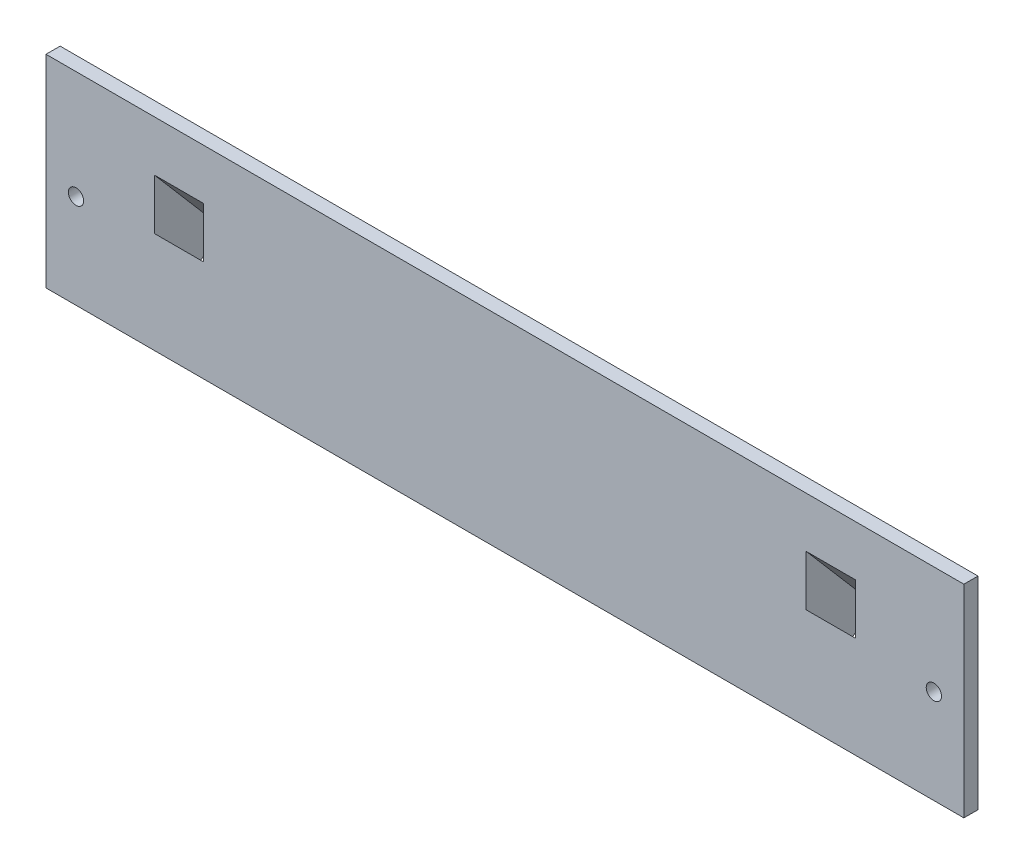
SolidWorks part; units mm, degrees
ref_plane "Alzado" through (0, 0, 0) normal (0, 0, 1) x (1, 0, 0)
ref_plane "Planta" through (0, 0, 0) normal (0, 1, 0) x (1, 0, 0)
ref_plane "Vista lateral" through (0, 0, 0) normal (1, 0, 0) x (0, 0, -1)
sketch "Croquis1" plane through (0, 0, 0) normal (0, 0, 1) x (1, 0, 0)
  line L0 (-97.5, 0) -> (97.5, 0)
  line L1 (97.5, 0) -> (97.5, 38)
  line L2 (97.5, 38) -> (-97.5, 38)
  line L3 (0, 0) -> (0, 28.0598) construction
  line L4 (-97.5, 0) -> (-97.5, 38)
  circle A2 centre (91.125, 15) radius 1.625
  circle A3 centre (-91.125, 15) radius 1.625
  point P13 (0, 38)
  point P14 (0, 0)
  dimension "D1" = 3.25
  dimension "D2" = 15
  dimension "D3" = 97.5
  dimension "D4" = 38
  dimension "D5" = 6.375
extrude "Saliente-Extruir1" add sketch "Croquis1" along normal blind 3
sketch "Croquis2" plane through (97.5, 0, 0) normal (1, 0, 0) x (0, 0, -1)
  line L7 (3.4296, 3.6779) -> (15.1854, 13.7539)
  line L9 (0, 0) -> (0, 38) construction
  line L10 (-3, 0) -> (0, 0) construction
  line L11 (15.1854, 13.7539) -> (0, 31.471)
  line L12 (0, 31.471) -> (0, 0.7384)
  line L13 (3.4296, 3.6779) -> (0, 0.7384)
  dimension "D1" = 40.6
  dimension "D2" = 20
extrude "Saliente-Extruir2" add sketch "Croquis2" against normal blind 16.5 from offset 20 offset against normal yes
sketch "Croquis3" plane through (0, 0.4257, 0.3649) normal (0, -0.7593, -0.6508) x (1, 0, 0)
  line L0 (61, -20.4805) -> (61, -0.4805) construction
  line L1 (64, -8.4805) -> (74.5, -8.4805)
  line L2 (64, -8.4805) -> (64, -15.4805)
  line L3 (64, -15.4805) -> (74.5, -15.4805)
  line L4 (74.5, -8.4805) -> (74.5, -15.4805)
  line L5 (61, -20.4805) -> (77.5, -20.4805) construction
  dimension "D1" = 10.5
  dimension "D2" = 3
  dimension "D3" = 5
  dimension "D4" = 7
extrude "Cortar-Extruir1" cut sketch "Croquis3" against normal through all
sketch "Croquis4" plane through (-97.5, 0, 0) normal (-1, 0, 0) x (0, 0, 1)
  line L0 (0, 0.7384) -> (-15.1854, 13.7539)
  line L1 (-15.1854, 13.7539) -> (0, 31.471)
  line L2 (0, 38) -> (0, 0) construction
  line L3 (0, 0.7384) -> (0, 31.471) construction
  line L4 (0, 31.471) -> (0, 0.7384)
extrude "Saliente-Extruir3" add sketch "Croquis4" against normal blind 16.5 from offset 20 offset against normal yes
sketch "Croquis5" plane through (0, 0.4257, 0.3649) normal (0, -0.7593, -0.6508) x (1, 0, 0)
  line L0 (-61, -20.4805) -> (-61, -0.4805) construction
  line L1 (-64, -15.4805) -> (-74.5, -15.4805)
  line L2 (-64, -15.4805) -> (-64, -8.4805)
  line L3 (-64, -8.4805) -> (-74.5, -8.4805)
  line L4 (-74.5, -15.4805) -> (-74.5, -8.4805)
  line L5 (64, -15.4805) -> (74.5, -15.4805) construction
  dimension "D1" = 3
  dimension "D2" = 10.5
  dimension "D3" = 7
extrude "Cortar-Extruir2" cut sketch "Croquis5" against normal through all
sketch "Croquis6" plane through (97.5, 0, 0) normal (1, 0, 0) x (0, 0, -1)
  line L0 (0, 0.7384) -> (15.1854, 13.7539)
  line L1 (15.1854, 13.7539) -> (0, 31.471)
  line L2 (0, 31.471) -> (0, 0.7384)
extrude "Saliente-Extruir4" add sketch "Croquis6" along normal blind 45 from offset 120 offset against normal yes
sketch "Croquis7" plane through (0, 0.4257, 0.3649) normal (0, -0.7593, -0.6508) x (1, 0, 0)
  line L0 (-22.5, -20.4805) -> (-22.5, -0.4805) construction
  circle A0 centre (-12.92, -10.4805) radius 8.25
  circle A1 centre (12.93, -10.4805) radius 8.25
  dimension "D1" = 16.5
  dimension "D2" = 25.85
  dimension "D3" = 9.58
extrude "Cortar-Extruir3" cut sketch "Croquis7" against normal through all
sketch "Croquis8" plane through (0, 0, 0) normal (0, -1, 0) x (1, 0, 0)
  line L1 (-97.5, 3) -> (97.5, 3)
  line L2 (-97.5, 3) -> (-97.5, 0)
  line L3 (-97.5, 0) -> (97.5, 0)
  line L4 (97.5, 3) -> (97.5, 0)
extrude "Saliente-Extruir5" add sketch "Croquis8" along normal blind 5
sketch "Croquis9" plane through (-22.5, 0, 0) normal (-1, 0, 0) x (0, 0, 1)
  line L0 (0, 0.7384) -> (-15.1854, 13.7539)
  line L1 (-15.1854, 13.7539) -> (0, 31.471)
  line L2 (0, 31.471) -> (0, 0.7384)
extrude "Cortar-Extruir4" cut sketch "Croquis9" against normal up to next
sketch "Croquis10" plane through (0, 0, 3) normal (0, 0, 1) x (1, 0, 0)
  line L1 (-29.0793, 34.7608) -> (26.5961, 34.7608)
  line L2 (-29.0793, 34.7608) -> (-29.0793, 2.1564)
  line L3 (-29.0793, 2.1564) -> (26.5961, 2.1564)
  line L4 (26.5961, 34.7608) -> (26.5961, 2.1564)
extrude "Saliente-Extruir7" add sketch "Croquis10" against normal blind 3
